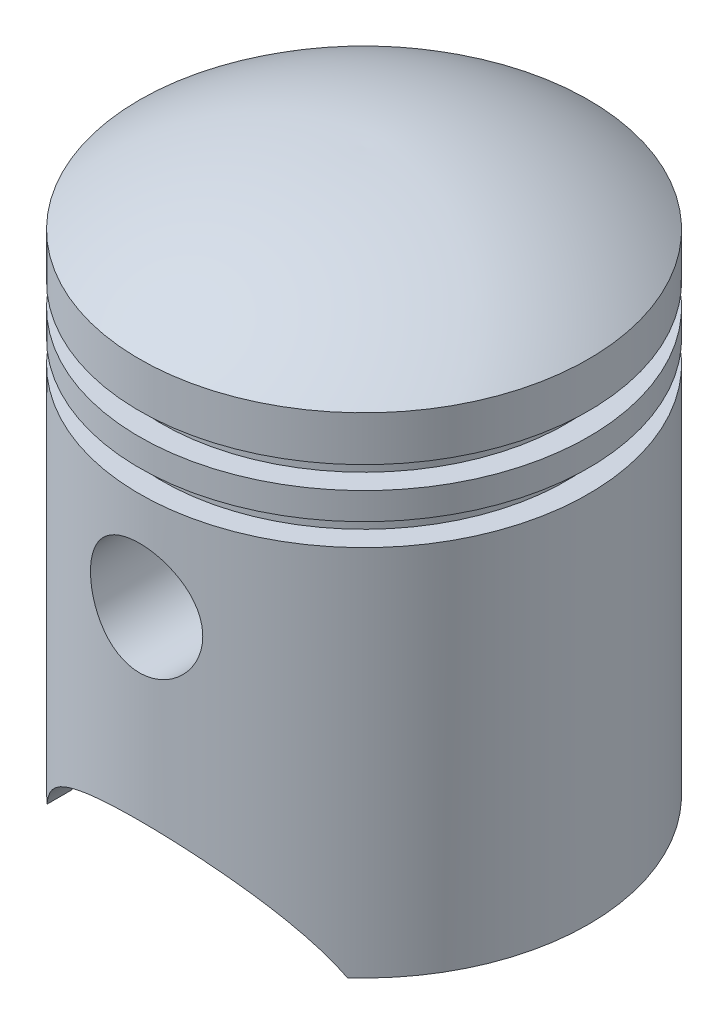
SolidWorks part; units mm, degrees
ref_plane "Front Plane" through (0, 0, 0) normal (0, 0, 1) x (1, 0, 0)
ref_plane "Top Plane" through (0, 0, 0) normal (0, 1, 0) x (1, 0, 0)
ref_plane "Right Plane" through (0, 0, 0) normal (1, 0, 0) x (0, 0, -1)
sketch "Sketch1" plane through (0, 0, 0) normal (0, 0, 1) x (1, 0, 0)
  line L0 (25, 0) -> (25, 41.5)
  line L1 (0, 62.5) -> (0, 0)
  line L2 (25, 0) -> (23, 0)
  line L3 (25, 49.5) -> (22.5, 49.5)
  line L4 (22.5, 49.5) -> (22.5, 47)
  line L5 (22.5, 47) -> (25, 47)
  line L6 (25, 49.5) -> (25, 54.5)
  line L7 (25, 44) -> (22.5, 44)
  line L8 (22.5, 44) -> (22.5, 41.5)
  line L9 (22.5, 41.5) -> (25, 41.5)
  line L10 (25, 44) -> (25, 47)
  line L11 (23, 0) -> (23, 39.5)
  line L12 (20.5, 39.5) -> (23, 39.5)
  line L14 (20.5, 45.5) -> (20.5, 45.5)
  line L15 (20.5, 45.5) -> (20.5, 45.5)
  line L16 (20.5, 45.5) -> (20.5, 45.5)
  line L18 (23, 51.5) -> (20.5, 51.5)
  line L19 (23, 51.5) -> (23, 53.4845)
  line L22 (23, 2) -> (2, 2) construction
  line L23 (2, 60.4985) -> (2, 2) construction
  line L24 (20.5, 51.5) -> (20.5, 45.5) construction
  line L25 (20.5, 45.5) -> (20.5, 39.5) construction
  line L26 (20.5, 51.5) -> (20.5, 39.5)
  line L27 (23, 2) -> (23, 39.5) construction
  line L28 (25, 0) -> (0, 0) construction
  arc A0 (25, 54.5) -> (0, 62.5) centre (0.9839, 22.5121) ccw
  arc A1 (23, 53.4845) -> (0, 60.4994) centre (0.9839, 22.5121) ccw
  arc A2 (23, 53.4845) -> (2, 60.4985) centre (0.9839, 22.5121) ccw construction
  dimension "D3" = 40
  dimension "D1" = 54.5
  dimension "D2" = 62.5
  dimension "D4" = 25
  dimension "D5" = 5
  dimension "D6" = 2.5
  dimension "D7" = 3
  dimension "D8" = 2.5
  dimension "D10" = 2.5
  dimension "D9" = 2
revolve "Revolve1" add sketch "Sketch1" angle 360 about L1
sketch "Sketch2" plane through (0, 0, 0) normal (0, 0, 1) x (1, 0, 0)
  line L0 (-25, 0) -> (25, 0) construction
  line L2 (-25, 0) -> (25, 0)
  circle A0 centre (0, 30.5) radius 6.25
  arc A1 (16.7332, 0) -> (-16.7332, 0) centre (0, -9) ccw
  point P3 (0, 10)
  dimension "D1" = 12.5
  dimension "D3" = 38
  dimension "D4" = 10
  dimension "D2" = 32
extrude "Cut-Extrude1" cut sketch "Sketch2" against normal through all both and the other way through all contours A0 | L2 A1
sketch "Sketch3" plane through (0, 0, 0) normal (0, 0, 1) x (1, 0, 0)
  circle A0 centre (0, 30.5) radius 6.25 construction
  circle A1 centre (0, 30.5) radius 6.25
  circle A2 centre (0, 30.5) radius 7.25
  dimension "D1" = 14.5
extrude "Boss-Extrude4" add sketch "Sketch3" along normal up to surface (11.4257 mm away) from offset 12.5 contours A2 A1
mirror "Mirror1" about plane through (0, 0, 0) normal (0, 0, 1) of "Boss-Extrude4"
